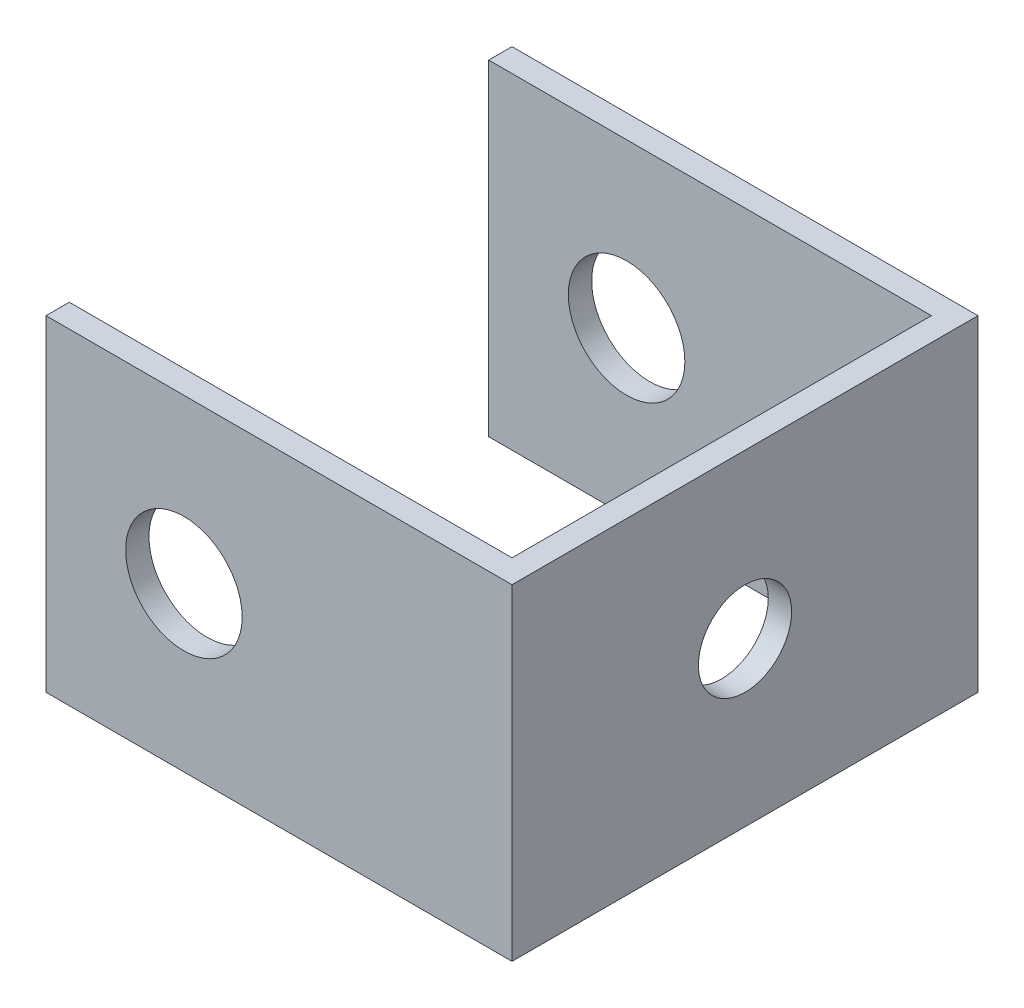
SolidWorks part; units mm, degrees
ref_plane "Front Plane" through (0, 0, 0) normal (0, 0, 1) x (1, 0, 0)
ref_plane "Top Plane" through (0, 0, 0) normal (0, 1, 0) x (1, 0, 0)
ref_plane "Right Plane" through (0, 0, 0) normal (1, 0, 0) x (0, 0, -1)
sketch "Sketch1" plane through (0, 0, 0) normal (0, 1, 0) x (1, 0, 0)
  line L1 (10, -10) -> (-10, -10)
  line L2 (10, -10) -> (10, 10)
  line L3 (10, 10) -> (-10, 10)
  line L4 (-10, -10) -> (-10, 10)
  line L5 (10, -10) -> (-10, 10) construction
  line L6 (10, 10) -> (-10, -10) construction
  line L7 (-10, 9) -> (9, 9)
  line L8 (-10, 9) -> (-10, -9)
  line L9 (-10, -9) -> (9, -9)
  line L10 (9, 9) -> (9, -9)
  line L11 (-0.5, -9) -> (-0.5, 9) construction
  line L12 (-10, 0) -> (9, 0) construction
  point P0 (0, 0)
  point P198 (-0.5, 0)
  dimension "D1" = 20
  dimension "D2" = 1
  dimension "D3" = 1
  dimension "D4" = 1
extrude "Boss-Extrude1" add sketch "Sketch1" along normal blind 14 contours L7 L10 L9 L4 L1 L2 L3
sketch "Sketch2" plane through (0, 0, 10) normal (0, 0, 1) x (1, 0, 0)
  circle A0 centre (-4.0817, 7) radius 2.5
  dimension "D1" = 5
extrude "Cut-Extrude1" cut sketch "Sketch2" against normal up to surface (20 mm away) up to face at (0, 7, -10)
sketch "Sketch3" plane through (10, 0, 0) normal (1, 0, 0) x (0, 0, -1)
  circle A0 centre (0, 7) radius 2
  dimension "D1" = 4
extrude "Cut-Extrude2" cut sketch "Sketch3" against normal up to next
